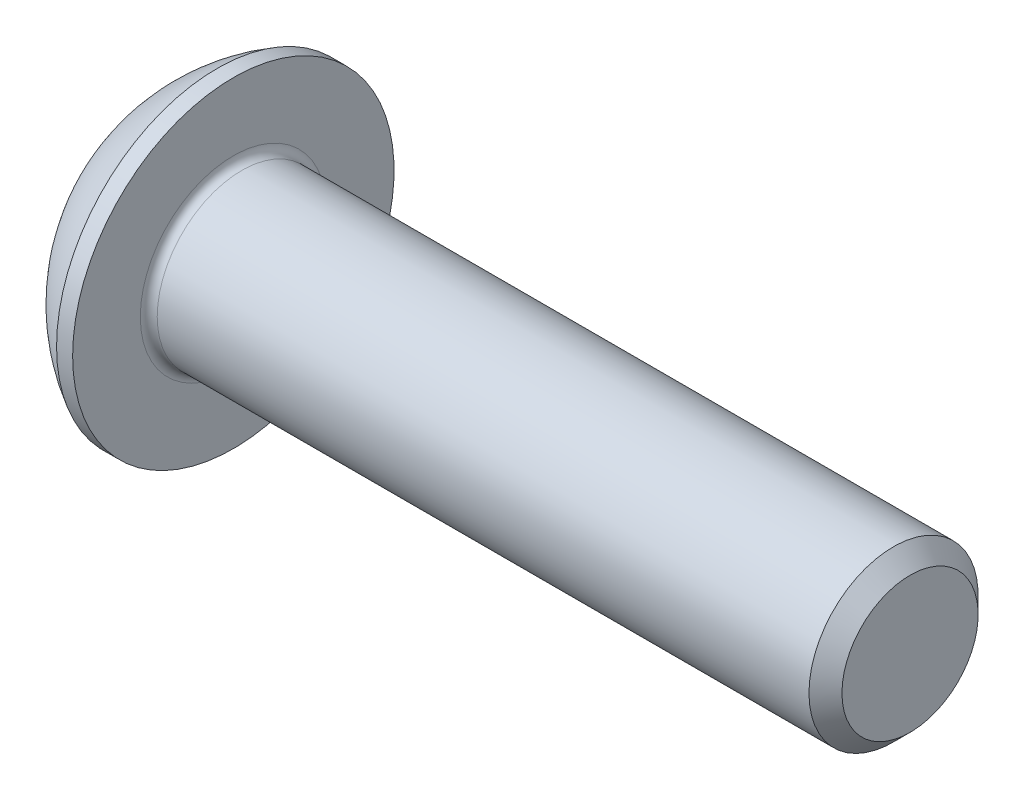
SolidWorks part; units mm, degrees
ref_plane "Plane1" through (0, 0, 0) normal (0, 0, 1) x (1, 0, 0)
ref_plane "Plane2" through (0, 0, 0) normal (0, 1, 0) x (1, 0, 0)
ref_plane "Plane3" through (0, 0, 0) normal (1, 0, 0) x (0, 0, -1)
revolve "BaseBody" add sketch "BodySke" angle 360 about L4
sketch "BodySke" plane through (0, 0, 0) normal (0, 0, 1) x (1, 0, 0)
  line L0 (18.2, 0) -> (18.2, 1.61)
  line L1 (17.81, 2) -> (2.2, 2)
  line L2 (2.2, 2) -> (2.2, 3.8)
  line L3 (2.2, 3.8) -> (1.82, 3.8)
  line L4 (0, 0) -> (101.6, 0) construction
  line L5 (2.2, -3.8) -> (1.82, -3.8) construction
  line L6 (55.6768, -2) -> (2.2, -2) construction
  line L7 (18.2, 0) -> (0, 0)
  line L8 (0, 1.9) -> (0, -1.9) construction
  line L9 (0, 0) -> (0, 1.9)
  line L10 (18.2, 1.61) -> (17.81, 2)
  line L11 (18.2, -1.61) -> (17.81, -2) construction
  line L12 (2.9, 9.525) -> (2.9, -2) construction
  line L13 (2.2, 9.525) -> (2.2, -2) construction
  arc A1 (0, 1.9) -> (1.82, 3.8) centre (3.8853, 0) cw
  dimension "D1" = 3.8
  dimension "Diameter" = 4
  dimension "Length" = 16
  dimension "Head_dia" = 7.6
  dimension "Head_ht" = 2.2
  dimension "Head_side_ht" = 0.38
  dimension "Minor_dia" = 3.22
  dimension "Body_ch_ang" = 45
  dimension "Advance" = 0.7
  dimension "Thread_nom" = 16
cosmetic thread "ThreadCosmetic" [suppressed] parameters "Thread_length"=14.6, "Thread_minor"=3.22
fillet "Fillet1" radius 0.2 1 edges at (2.2, 0, 2)
sketch "Sketch2" plane through (0, 0, 0) normal (0, 0, 1) x (1, 0, 0)
  line L0 (0, 1.25) -> (1.3, 1.25)
  line L1 (1.3, 1.25) -> (2.0217, 0)
  line L3 (2.0217, 0) -> (0, 0)
  line L4 (0, 0) -> (0, 1.25)
  line L5 (0, -1.25) -> (1.3, -1.25) construction
  line L6 (0, 0) -> (47.625, 0) construction
  dimension "D2" = 60
  dimension "PreBroach_depth" = 1.3
  dimension "PreBroach_dia" = 2.5
revolve "PreBroach" cut sketch "Sketch2" angle 360 about L6
sketch "Sketch3" plane through (0, 0, 0) normal (1, 0, 0) x (0, 0, -1)
  line L0 (-1.25, -0.7217) -> (-1.25, 0.7217)
  line L1 (-1.25, 0.7217) -> (0, 1.4434)
  line L2 (0, 1.4434) -> (1.25, 0.7217)
  line L3 (1.25, 0.7217) -> (1.25, -0.7217)
  line L4 (1.25, -0.7217) -> (0, -1.4434)
  line L5 (0, -1.4434) -> (-1.25, -0.7217)
  dimension "D1" = 1.25
  dimension "D2" = 1.25
  dimension "D3" = 2.5
  dimension "Hex_size" = 2.5
extrude "Hex" cut sketch "Sketch3" along normal blind 1.3
sketch "ThdSchSke" plane through (0, 0, 0) normal (0, 0, 1) x (1, 0, 0)
  line L0 (3.6, -1.61) -> (3.3269, -2)
  line L1 (3.6, -1.61) -> (3.8731, -2)
  line L2 (3.8731, -2) -> (3.8731, -2.5)
  line L3 (-3.175, 0) -> (5.1513, 0) construction
  line L5 (3.8731, -2.5) -> (3.3269, -2.5)
  line L6 (3.3269, -2.5) -> (3.3269, -2)
  dimension "Thread_minor" = 3.22
  dimension "Diameter" = 4
  dimension "Start" = 3.6
  dimension "SideAngle" = 55
  dimension "VeeAngle" = 70
  dimension "Overcut" = 5
revolve "ThreadSchematic" [suppressed] cut sketch "ThdSchSke" angle 360 about L3
pattern_linear "ThdSchPat" [suppressed]
equation "\"D1@BodySke\" = \"Head_dia@BodySke\" * .5"
equation "\"Thread_minor@ThreadCosmetic\" = \"Minor_dia@BodySke\""
equation "\"D1@Sketch3\" = \"Hex_size@Sketch3\" / 2"
equation "\"D2@Sketch3\" = \"D1@Sketch3\""
equation "\"D3@Sketch3\" = \"Hex_size@Sketch3\""
equation "\"Thread_length@ThreadCosmetic\" = ((sgn( (\"Length@BodySke\" - \"Advance@BodySke\" * 2.0) - \"Thread_nom@BodySke\" )-1)*( (\"Length@BodySke\" - \"Advance@BodySke\" * 2.0) - \"Thread_nom@BodySke\" ))/-2+ \"Thread_nom@BodySke\""
equation "\"Thread_minor@ThdSchSke\" = \"Minor_dia@BodySke\""
equation "\"Diameter@ThdSchSke\" = \"Diameter@BodySke\""
equation "\"Overcut@ThdSchSke\" = \"Diameter@BodySke\" * 1.25"
equation "\"Start@ThdSchSke\" = \"Head_ht@BodySke\" + \"Length@BodySke\" - \"Thread_length@ThreadCosmetic\"  '---Non-countersunk---"
equation "\"Num_threads@ThdSchPat\" = int( \"Thread_length@ThreadCosmetic\" / \"Advance@BodySke\" + 0.999 )  + 1"
equation "\"Advance@ThdSchPat\" = \"Thread_length@ThreadCosmetic\" /  (\"Num_threads@ThdSchPat\" - 1) 'relax it"
equation "\"Num_threads@ThdSchPat\" = \"Num_threads@ThdSchPat\" - sgn( \"Num_threads@ThdSchPat\" - 1) '---chamfered tips only---"
